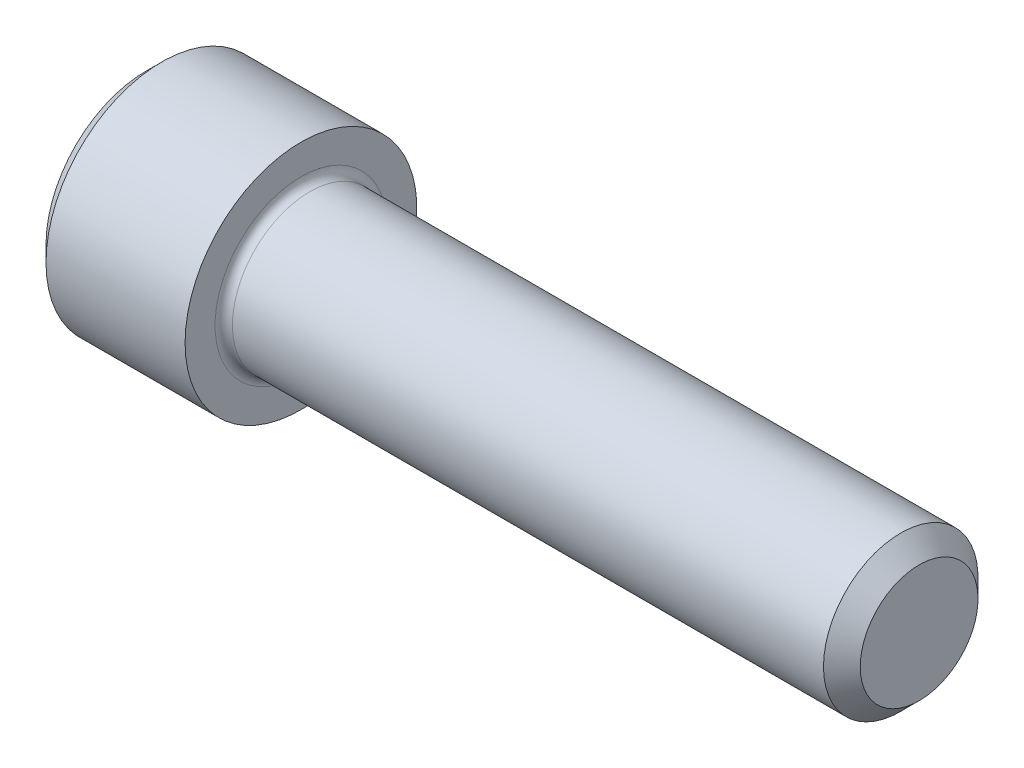
SolidWorks part; units mm, degrees
ref_plane "Plane1" through (0, 0, 0) normal (0, 0, 1) x (1, 0, 0)
ref_plane "Plane2" through (0, 0, 0) normal (0, 1, 0) x (1, 0, 0)
ref_plane "Plane3" through (0, 0, 0) normal (1, 0, 0) x (0, 0, -1)
sketch "BodySke" plane through (0, 0, 0) normal (0, 0, 1) x (1, 0, 0)
  line L0 (0, 0) -> (0, 4.1275)
  line L1 (0.635, 4.7625) -> (6.35, 4.7625)
  line L2 (6.35, 4.7625) -> (6.35, 3.175)
  line L3 (6.35, 3.175) -> (30.9944, 3.175)
  line L4 (31.75, 2.4193) -> (31.75, 0)
  line L5 (31.75, 0) -> (0, 0)
  line L6 (-31.75, 0) -> (127, 0) construction
  line L7 (0, 4.1275) -> (0.635, 4.7625)
  line L8 (31.75, 2.4193) -> (30.9944, 3.175)
  line L9 (0, -4.1275) -> (0.635, -4.7625) construction
  line L10 (31.75, -2.4193) -> (30.9944, -3.175) construction
  line L11 (7.62, 9.525) -> (7.62, 3.175) construction
  line L12 (6.35, 9.525) -> (6.35, 3.175) construction
  line L13 (-6.35, 9.525) -> (-6.35, 3.175) construction
  dimension "Diameter" = 6.35
  dimension "Head_ht" = 6.35
  dimension "Length" = 25.4
  dimension "Body_ch_ang" = 45
  dimension "Head_dia" = 9.525
  dimension "Head_ch_ang" = 45
  dimension "Head_side_ht" = 5.715
  dimension "Minor_dia" = 4.8387
  dimension "Advance" = 1.27
  dimension "Thread_nom" = 25.4
  dimension "Thread_length" = 38.1
revolve "Base-Revolve" add sketch "BodySke"
cosmetic thread "ThreadCosmetic" [suppressed]
fillet "Fillet1" radius 0.3556 1 edges at (6.35, 0, 3.175)
sketch "Sketch2" plane through (0, 0, 0) normal (0, 0, 1) x (1, 0, 0)
  line L0 (0, 2.3813) -> (3.048, 2.3813)
  line L1 (3.048, 2.3813) -> (4.4228, 0)
  line L2 (-31.75, 0) -> (127, 0) construction
  line L3 (4.4228, 0) -> (0, 0)
  line L4 (0, 0) -> (0, 2.3813)
  line L5 (0, 4.1275) -> (0, -4.1275) construction
  line L6 (0, 0) -> (47.625, 0) construction
  line L7 (6.35, -4.7625) -> (6.35, 4.7625) construction
  dimension "D1" = 2.3813
  dimension "D2" = 60
  dimension "Wall_thickness" = 3.302
revolve "Hex-PreBroach" cut sketch "Sketch2" angle 360 about L6
sketch "Sketch3" plane through (0, 0, 0) normal (-1, 0, 0) x (0, 0.5, 0.866)
  line L0 (1.3748, 2.3813) -> (-1.3748, 2.3813)
  line L1 (-1.3748, 2.3813) -> (-2.7496, 0)
  line L2 (1.3748, 2.3813) -> (2.7496, 0)
  line L3 (1.3748, -2.3812) -> (2.7496, 0)
  line L4 (1.3748, -2.3812) -> (-1.3748, -2.3812)
  line L5 (-1.3748, -2.3812) -> (-2.7496, 0)
  dimension "D1" = 2.3813
  dimension "D2" = 2.3813
  dimension "Hex_size" = 4.7625
extrude "Hex" cut sketch "Sketch3" against normal blind 3.048
sketch "Sketch4" plane through (0, 0, 0) normal (-1, 0, 0) x (0, 0, 1)
  line L0 (0, 0) -> (2.8067, 0)
  line L1 (0, 0) -> (6.1484, 3.5498) construction
  line L2 (0, 0) -> (1.4033, 2.4307)
  line L3 (2.3336, 0.614) -> (2.6851, 0.817)
  line L4 (1.6986, 1.7139) -> (2.0501, 1.9169)
  arc A0 (2.3336, 0.614) -> (1.6986, 1.7139) centre (0, 0) ccw
  arc A1 (2.8067, 0) -> (2.6851, 0.817) centre (0, 0) ccw
  arc A2 (1.4033, 2.4307) -> (2.0501, 1.9169) centre (0, 0) cw
  dimension "D1" = 30
  dimension "Spline_n_dim" = 4.826
  dimension "Spline_m_dim" = 5.6134
  dimension "D2" = 60
  dimension "D3" = 0.635
  dimension "Spline_p_dim" = 1.27
extrude "Spline" [suppressed] cut sketch "Sketch4" against normal blind 3.048
pattern_circular "CirPattern1" [suppressed] count 6 every 60
sketch "Sketch5" plane through (0, 0, 0) normal (0, 0, 1) x (1, 0, 0)
  line L0 (-31.75, 0) -> (127, 0) construction
  line L2 (0, 4.1275) -> (0, -4.1275) construction
  circle A0 centre (2.159, 0) radius 0.5905
  dimension "Drilled_hole_dia" = 1.1811
  dimension "Drilled_hole_loc" = 2.159
extrude "Hole" [suppressed] cut sketch "Sketch5" against normal through all and the other way through all
pattern_circular "Drilled-4" [suppressed] count 2 every 60
pattern_circular "Drilled-6" [suppressed] count 3 every 60
sketch "ThdSchSke" plane through (0, 0, 0) normal (0, 0, 1) x (1, 0, 0)
  line L0 (7.62, -2.4193) -> (7.0909, -3.175)
  line L1 (7.62, -2.4193) -> (8.1491, -3.175)
  line L2 (8.1491, -3.175) -> (8.1491, -3.9687)
  line L3 (-3.175, 0) -> (5.1513, 0) construction
  line L5 (8.1491, -3.9687) -> (7.0909, -3.9688)
  line L6 (7.0909, -3.9688) -> (7.0909, -3.175)
  line L7 (0, 4.1275) -> (0, -4.1275) construction
  dimension "Thread_minor" = 4.8387
  dimension "Diameter" = 6.35
  dimension "Start" = 7.62
  dimension "SideAngle" = 55
  dimension "VeeAngle" = 70
  dimension "Overcut" = 7.9375
revolve "ThreadSchematic" [suppressed] cut sketch "ThdSchSke" angle 360 about L3
pattern_linear "ThdSchPat" [suppressed]
equation "\"D2@Sketch3\" = \"Hex_size@Sketch3\" / 2"
equation "\"D1@Sketch3\" = \"Hex_size@Sketch3\" / 2"
equation "\"D1@Sketch2\" = \"Hex_size@Sketch3\" / 2"
equation "\"D3@Sketch4\" = \"Spline_p_dim@Sketch4\" / 2"
equation "\"Thread_minor@ThreadCosmetic\"  =  \"Minor_dia@BodySke\""
equation "\"D2@CirPattern1\" = 360 / \"Num_teeth@CirPattern1\""
equation "\"Wall_thickness@Sketch2\" = \"Head_ht@BodySke\" - \"Key_eng@Hex\""
equation "\"Thread_length@ThreadCosmetic\" = ((sgn( (\"Length@BodySke\" - \"Advance@BodySke\" ) - \"Thread_nom@BodySke\" )-1)*( (\"Length@BodySke\" - \"Advance@BodySke\" ) - \"Thread_nom@BodySke\" ))/-2+ \"Thread_nom@BodySke\""
equation "\"Thread_minor@ThdSchSke\" = \"Minor_dia@BodySke\""
equation "\"Diameter@ThdSchSke\" = \"Diameter@BodySke\""
equation "\"Overcut@ThdSchSke\" = \"Diameter@BodySke\" * 1.25"
equation "\"Start@ThdSchSke\" = \"Head_ht@BodySke\" + \"Length@BodySke\" - \"Thread_length@ThreadCosmetic\"  '---Non-countersunk---"
equation "\"Num_threads@ThdSchPat\" = int( \"Thread_length@ThreadCosmetic\" / \"Advance@BodySke\" + 0.999 )  + 1"
equation "\"Advance@ThdSchPat\" = \"Thread_length@ThreadCosmetic\" /  (\"Num_threads@ThdSchPat\" - 1) 'relax it"
equation "\"Num_threads@ThdSchPat\" = \"Num_threads@ThdSchPat\" - sgn( \"Num_threads@ThdSchPat\" - 1) '---chamfered tips only---"
